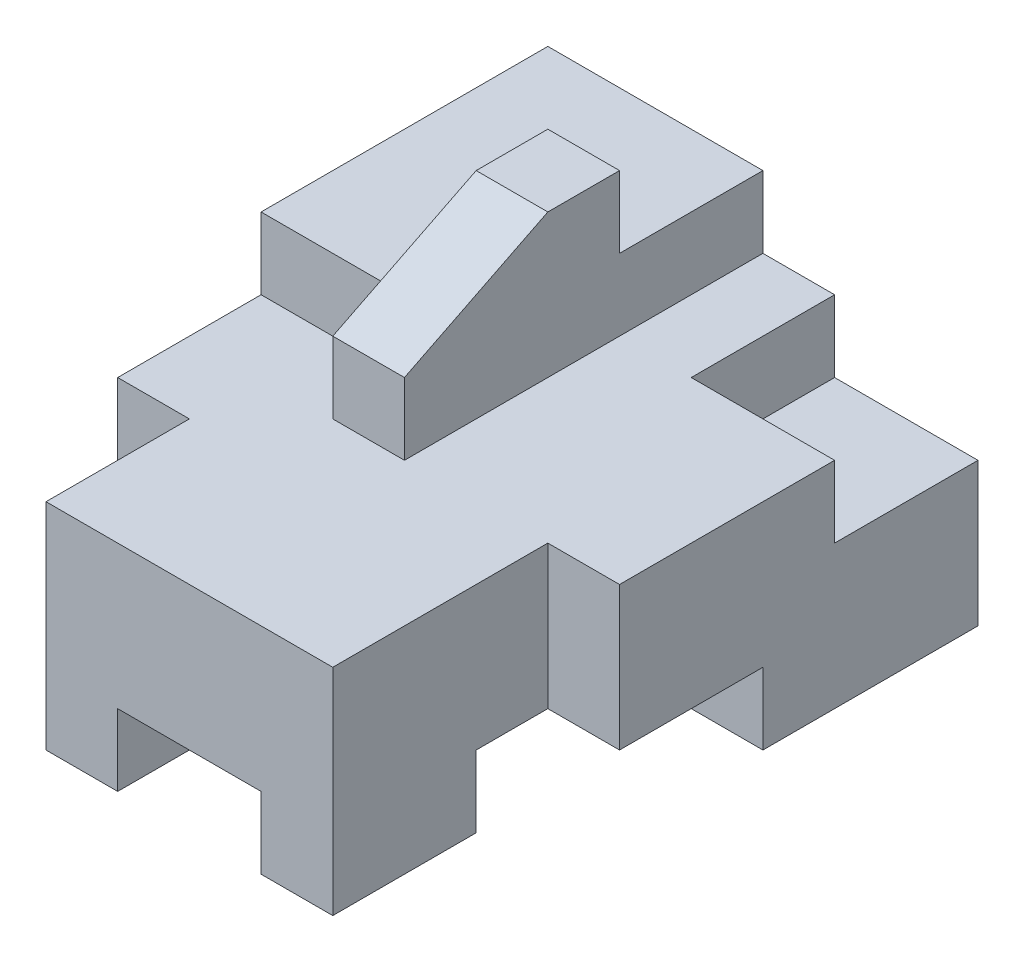
SolidWorks part; units mm, degrees
ref_plane "Front Plane" through (0, 0, 0) normal (0, 0, 1) x (1, 0, 0)
ref_plane "Top Plane" through (0, 0, 0) normal (0, 1, 0) x (1, 0, 0)
ref_plane "Right Plane" through (0, 0, 0) normal (1, 0, 0) x (0, 0, -1)
sketch "Sketch1" plane through (0, 0, 0) normal (0, 0, 1) x (1, 0, 0)
  line L1 (3, -2) -> (-3, -2)
  line L2 (3, -2) -> (3, 2)
  line L3 (3, 2) -> (-3, 2)
  line L4 (-3, -2) -> (-3, 2)
  line L5 (3, -2) -> (-3, 2) construction
  line L6 (3, 2) -> (-3, -2) construction
  point P0 (0, 0)
  dimension "D1" = 4
  dimension "D2" = 6
extrude "Boss-Extrude1" add sketch "Sketch1" along normal blind 8
sketch "Sketch2" plane through (0, 0, 8) normal (0, 0, 1) x (1, 0, 0)
  line L0 (-1, -2) -> (-1, -1)
  line L1 (-3, -2) -> (3, -2) construction
  line L2 (-1, -1) -> (1, -1)
  line L3 (1, -1) -> (1, -2)
  line L4 (1, -2) -> (-1, -2)
  dimension "D1" = 2
  dimension "D2" = 2
  dimension "D3" = 1
extrude "Cut-Extrude1" cut sketch "Sketch2" against normal through all
sketch "Sketch3" plane through (0, 2, 0) normal (0, 1, 0) x (1, 0, 0)
  line L0 (-2, -8) -> (-2, -6)
  line L1 (3, -8) -> (-3, -8) construction
  line L2 (-2, -6) -> (-3, -6)
  line L3 (-3, -8) -> (-3, 0) construction
  line L4 (-3, -6) -> (-3, -8)
  line L5 (-3, -8) -> (-2, -8)
  line L6 (3, -8) -> (2, -8)
  line L7 (2, -8) -> (2, -5)
  line L8 (2, -5) -> (3, -5)
  line L9 (3, -8) -> (3, 0) construction
  line L10 (3, -5) -> (3, -8)
  dimension "D1" = 1
  dimension "D2" = 1
  dimension "D3" = 2
  dimension "D4" = 3
extrude "Cut-Extrude2" cut sketch "Sketch3" against normal through all
sketch "Sketch4" plane through (3, 0, 0) normal (1, 0, 0) x (0, 0, -1)
  line L0 (-3, -2) -> (-3, -1)
  line L1 (-5, -2) -> (0, -2) construction
  line L2 (-3, -1) -> (-6, -1)
  line L3 (-6, -1) -> (-6, -2)
  line L4 (-5, -2) -> (-8, -2) construction
  line L5 (-6, -2) -> (-3, -2)
  dimension "D1" = 1
  dimension "D2" = 2
  dimension "D3" = 3
extrude "Cut-Extrude3" cut sketch "Sketch4" against normal through all
sketch "Sketch5" plane through (0, 2, 0) normal (0, 1, 0) x (1, 0, 0)
  line L0 (-3, 0) -> (0, 0)
  line L1 (3, 0) -> (-3, 0) construction
  line L2 (0, 0) -> (0, -5)
  line L3 (0, -5) -> (-1, -5)
  line L4 (-1, -5) -> (-1, -4)
  line L5 (-1, -4) -> (-3, -4)
  line L6 (-3, -6) -> (-3, 0) construction
  line L7 (-3, -4) -> (-3, 0)
  dimension "D1" = 3
  dimension "D2" = 4
  dimension "D3" = 1
  dimension "D4" = 1
extrude "Cut-Extrude4" cut sketch "Sketch5" against normal blind 1 flip side to cut
sketch "Sketch6" plane through (0, 1, 0) normal (0, 1, 0) x (1, 0, 0)
  line L0 (3, 0) -> (1, 0)
  line L1 (3, 0) -> (0, 0) construction
  line L2 (1, 0) -> (1, -2)
  line L3 (1, -2) -> (3, -2)
  line L4 (3, -5) -> (3, 0) construction
  line L5 (3, -2) -> (3, 0)
  dimension "D1" = 2
  dimension "D2" = 2
extrude "Cut-Extrude5" cut sketch "Sketch6" against normal blind 1
sketch "Sketch7" plane through (0, 2, 0) normal (0, 1, 0) x (1, 0, 0)
  line L0 (0, -5) -> (-1, -5)
  line L1 (-1, -5) -> (-1, -2)
  line L2 (-1, -2) -> (0, -2)
  line L3 (0, -5) -> (0, 0) construction
  line L4 (0, -2) -> (0, -5)
  line L5 (0, 0) -> (-3, 0) construction
  dimension "D1" = 2
extrude "Boss-Extrude2" add sketch "Sketch7" along normal blind 1
sketch "Sketch8" plane through (0, 0, 0) normal (1, 0, 0) x (0, 0, -1)
  line L0 (-3, 3) -> (-5, 2)
  line L1 (-5, 3) -> (-2, 3) construction
  line L2 (-5, 1) -> (-5, 3) construction
  line L3 (-5, 2) -> (-5, 3)
  line L4 (-5, 3) -> (-3, 3)
  dimension "D1" = 1
  dimension "D2" = 1
extrude "Cut-Extrude6" cut sketch "Sketch8" against normal through all
